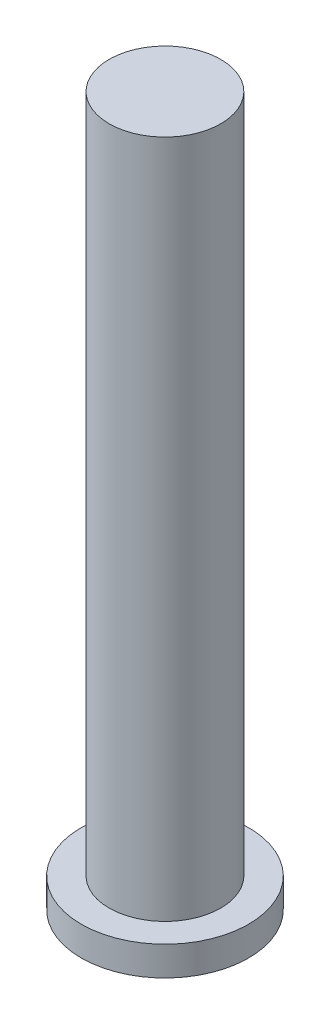
SolidWorks part; units mm, degrees
ref_plane "Front Plane" through (0, 0, 0) normal (0, 0, 1) x (1, 0, 0)
ref_plane "Top Plane" through (0, 0, 0) normal (0, 1, 0) x (1, 0, 0)
ref_plane "Right Plane" through (0, 0, 0) normal (1, 0, 0) x (0, 0, -1)
sketch "Sketch1" plane through (0, 0, 0) normal (0, 1, 0) x (1, 0, 0)
  circle A0 centre (0, 0) radius 1.5
  dimension "D1" = 3
extrude "Boss-Extrude1" add sketch "Sketch1" along normal blind 0.525
sketch "Sketch2" plane through (0, 0.525, 0) normal (0, 1, 0) x (1, 0, 0)
  circle A0 centre (0, 0) radius 1
  dimension "D1" = 2
extrude "Boss-Extrude2" add sketch "Sketch2" along normal blind 12.175
